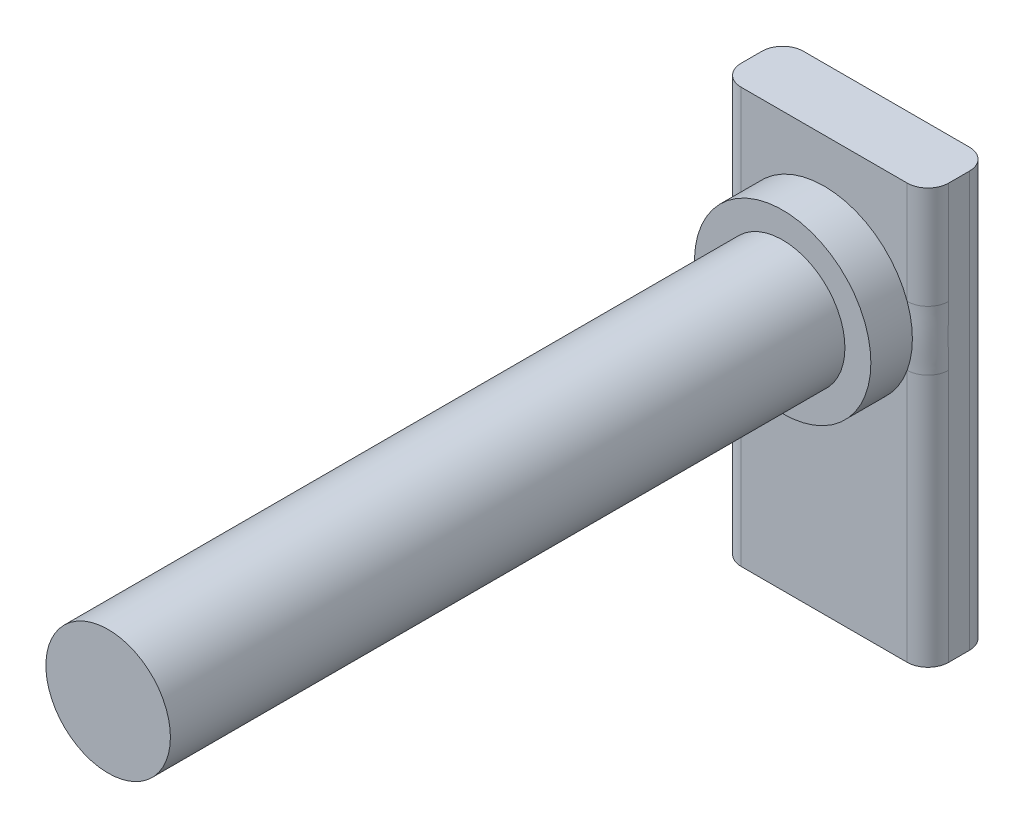
SolidWorks part; units mm, degrees
ref_plane "Front Plane" through (0, 0, 0) normal (0, 0, 1) x (1, 0, 0)
ref_plane "Top Plane" through (0, 0, 0) normal (0, 1, 0) x (1, 0, 0)
ref_plane "Right Plane" through (0, 0, 0) normal (1, 0, 0) x (0, 0, -1)
sketch "Sketch1" plane through (0, 0, 0) normal (0, 1, 0) x (1, 0, 0)
  line L1 (-10, 3) -> (10, 3)
  line L2 (-10, 3) -> (-10, -3)
  line L3 (-10, -3) -> (10, -3)
  line L4 (10, 3) -> (10, -3)
  point P5 (0, 3)
  point P7 (-10, 0)
  dimension "D1" = 6
  dimension "D2" = 20
extrude "Boss-Extrude1" add sketch "Sketch1" along normal blind 40
sketch "Sketch5" plane through (0, 0, 3) normal (0, 0, 1) x (1, 0, 0)
  line L0 (-10, 40) -> (10, 40) construction
  circle A0 centre (0, 27.25) radius 6
  dimension "D1" = 12
  dimension "D2" = 12.75
extrude "Boss-Extrude8" add sketch "Sketch5" along normal blind 69
sketch "Sketch8" plane through (0, 0, 3) normal (0, 0, 1) x (1, 0, 0)
  circle A0 centre (0, 27.25) radius 8.5
  dimension "D1" = 17
extrude "Boss-Extrude9" add sketch "Sketch8" along normal blind 4
fillet "Fillet1" radius 2 4 edges at (-10, 20, 3) (10, 20, 3) (-10, 20, -3) (10, 20, -3)
